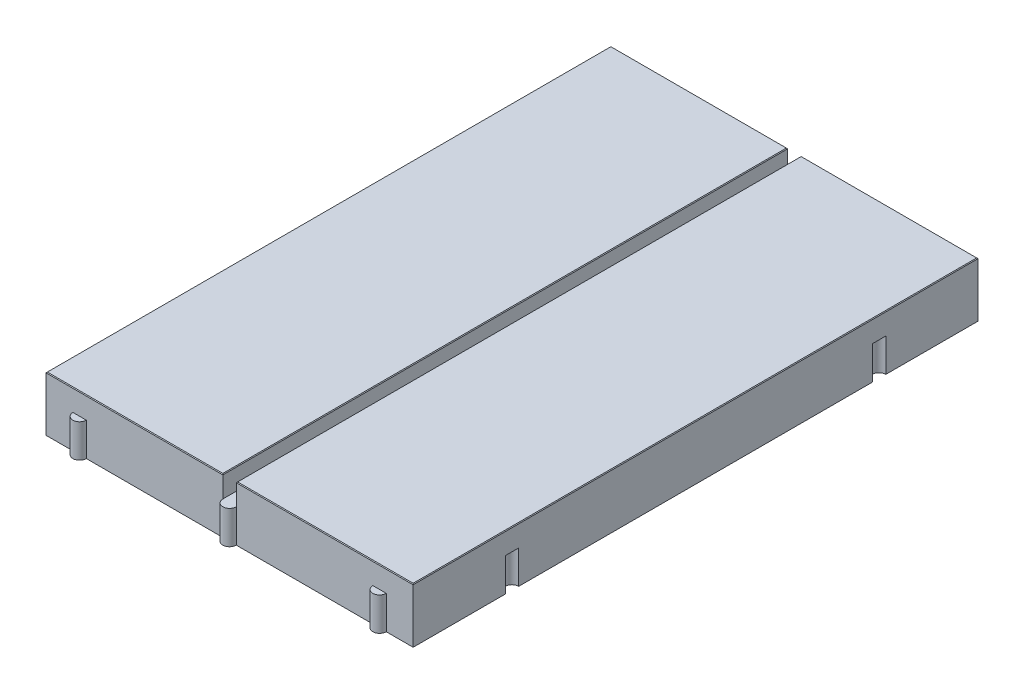
SolidWorks part; units mm, degrees
material "ABS"
ref_plane "Front Plane" through (0, 0, 0) normal (0, 0, 1) x (1, 0, 0)
ref_plane "Top Plane" through (0, 0, 0) normal (0, 1, 0) x (1, 0, 0)
ref_plane "Right Plane" through (0, 0, 0) normal (1, 0, 0) x (0, 0, -1)
sketch "Sketch1" plane through (0, 0, 0) normal (0, 1, 0) x (1, 0, 0)
  line L1 (-27.3, 42) -> (27.3, 42)
  line L2 (-27.3, 42) -> (-27.3, -42)
  line L3 (-27.3, -42) -> (27.3, -42)
  line L4 (27.3, 42) -> (27.3, -42)
  line L5 (-27.3, 42) -> (27.3, -42) construction
  line L6 (-27.3, -42) -> (27.3, 42) construction
  point P0 (0, 0)
  dimension "D1" = 54.6
  dimension "D2" = 84
extrude "Boss-Extrude1" add sketch "Sketch1" along normal blind 8.15
sketch "Sketch2" plane through (0, 8.15, 0) normal (0, 1, 0) x (1, 0, 0)
  line L0 (0, 42) -> (0, -42) construction
  line L1 (27.3, 42) -> (-27.3, 42) construction
  line L2 (-27.3, -42) -> (27.3, -42) construction
  line L4 (-1, -42) -> (1, -42)
  line L5 (-1, -42) -> (-1, 42)
  line L6 (-1, 42) -> (1, 42)
  line L7 (1, -42) -> (1, 42)
  line L8 (-1, -42) -> (1, 42) construction
  line L9 (-1, 42) -> (1, -42) construction
  point P6 (0, 0)
  dimension "D1" = 2
extrude "Cut-Extrude1" cut sketch "Sketch2" against normal blind 3.2
chamfer "Chamfer1" distance 0.1 angle 45 8 edges at (14.15, 8.15, -42) (27.3, 8.15, 0) (14.15, 8.15, 42) (1, 8.15, 0) (-14.15, 8.15, 42) (-27.3, 8.15, 0) (-14.15, 8.15, -42) (-1, 8.15, 0)
sketch "Sketch6" plane through (0, 0, 0) normal (0, 1, 0) x (1, 0, 0)
  line L0 (-27.3, -42) -> (-27.3, 42) construction
  line L1 (-27.3, 28.3) -> (-27.3, 26.3)
  line L2 (-27.3, 26.3) -> (-27.317, 26.2668)
  line L3 (-23.3, -42) -> (-21.3, -42)
  line L4 (-27.3, -26.3) -> (-27.3, -28.3)
  line L5 (-1, -42) -> (1, -42)
  line L6 (-1, -42) -> (1, -42) construction
  line L7 (-1, -42) -> (-27.3, -42) construction
  line L8 (21.3, -42) -> (23.3, -42)
  line L9 (27.3, -42) -> (1, -42) construction
  arc A0 (-27.3, 28.3) -> (-27.3, 26.3) centre (-27.3, 27.3) ccw
  arc A1 (-27.3, -26.3) -> (-27.3, -28.3) centre (-27.3, -27.3) ccw
  arc A2 (-23.3, -42) -> (-21.3, -42) centre (-22.3, -42) ccw
  arc A3 (-1, -42) -> (1, -42) centre (0, -42) ccw
  arc A4 (21.3, -42) -> (23.3, -42) centre (22.3, -42) ccw
  dimension "D9" = 1
  dimension "D1" = 2
  dimension "D2" = 13.7
  dimension "D3" = 2
  dimension "D4" = 13.7
  dimension "D5" = 4
  dimension "D6" = 2
  dimension "D7" = 2
  dimension "D8" = 4
extrude "Boss-Extrude2" add sketch "Sketch6" along normal up to surface (4.95 mm away) contours L8 A4 | L5 A3 up to face at (0, 4.95, 0)
sketch "Sketch13" plane through (0, 0, 0) normal (0, 1, 0) x (1, 0, 0)
  line L0 (27.3, 42) -> (27.3, -42) construction
  line L1 (27.3, 28.3) -> (27.3, 26.3)
  line L3 (-23.3, 42) -> (-21.3, 42)
  line L4 (27.3, -26.3) -> (27.3, -28.3)
  line L5 (-1, 42) -> (1, 42)
  line L6 (-27.3, -28.3) -> (27.3, -28.3) construction
  line L7 (-27.3, -26.3) -> (-27.3, -28.3) construction
  line L8 (21.3, 42) -> (23.3, 42)
  line L9 (1, 42) -> (-1, 42) construction
  line L10 (-27.3, 28.3) -> (27.3, 28.3) construction
  line L11 (-27.3, -42) -> (-27.3, 42) construction
  line L12 (27.3, -42) -> (27.3, 42) construction
  arc A0 (27.3, 28.3) -> (27.3, 26.3) centre (27.3, 27.3) ccw
  arc A1 (27.3, -26.3) -> (27.3, -28.3) centre (27.3, -27.3) ccw
  arc A2 (-23.3, 42) -> (-21.3, 42) centre (-22.3, 42) ccw
  arc A3 (-1, 42) -> (1, 42) centre (0, 42) ccw
  arc A4 (21.3, 42) -> (23.3, 42) centre (22.3, 42) ccw
  arc A5 (-27.3, 28.3) -> (-27.3, 26.3) centre (-27.3, 27.3) ccw construction
  dimension "D9" = 1
  dimension "D1" = 2
  dimension "D2" = 4
  dimension "D3" = 2
  dimension "D4" = 4
  dimension "D6" = 2
  dimension "D7" = 2
extrude "Cut-Extrude4" cut sketch "Sketch13" along normal up to surface (4.95 mm away) up to face at (0, 4.95, 0.25)
